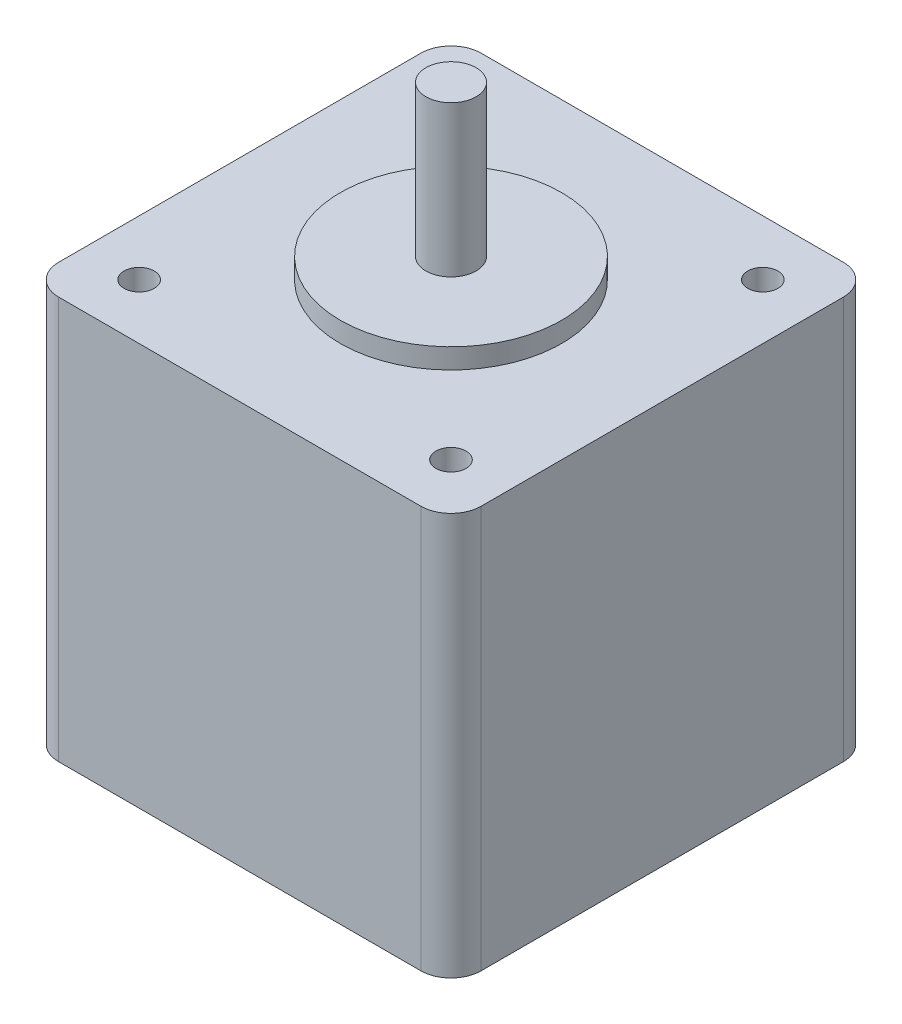
SolidWorks part; units mm, degrees
material "Rubber"
ref_plane "Front Plane" through (0, 0, 0) normal (0, 0, 1) x (1, 0, 0)
ref_plane "Top Plane" through (0, 0, 0) normal (0, 1, 0) x (1, 0, 0)
ref_plane "Right Plane" through (0, 0, 0) normal (1, 0, 0) x (0, 0, -1)
sketch "Sketch1" plane through (0, 0, 0) normal (0, 1, 0) x (1, 0, 0)
  line L1 (3, 0) -> (39, 0)
  line L2 (0, 3) -> (0, 39)
  line L3 (3, 42) -> (39, 42)
  line L4 (42, 3) -> (42, 39)
  arc A0 (39, 42) -> (42, 39) centre (39, 39) cw
  arc A1 (39, 0) -> (42, 3) centre (39, 3) ccw
  arc A2 (3, 0) -> (0, 3) centre (3, 3) cw
  arc A3 (0, 39) -> (3, 42) centre (3, 39) cw
  point P11 (0, 0)
  dimension "D1" = 3
extrude "Boss-Extrude1" add sketch "Sketch1" along normal blind 40
sketch "Sketch2" plane through (0, 40, 0) normal (0, 1, 0) x (1, 0, 0)
  line L1 (0, 39) -> (0, 3) construction
  line L2 (39, 42) -> (3, 42) construction
  circle A0 centre (21, 21) radius 11
  dimension "D1" = 21
  dimension "D2" = 21
extrude "Boss-Extrude2" add sketch "Sketch2" along normal blind 2
sketch "Sketch3" plane through (0, 42, 0) normal (0, 1, 0) x (1, 0, 0)
  circle A0 centre (21, 21) radius 2.5
extrude "Boss-Extrude3" add sketch "Sketch3" along normal blind 15
sketch "Sketch4" plane through (0, 40, 0) normal (0, 1, 0) x (1, 0, 0)
  line L2 (0, 39) -> (0, 3) construction
  line L4 (39, 42) -> (3, 42) construction
  circle A0 centre (5.5, 36.5) radius 1.5
  circle A1 centre (36.5, 36.5) radius 1.5
  circle A2 centre (36.5, 5.5) radius 1.5
  circle A3 centre (5.5, 5.5) radius 1.5
  dimension "D1" = 5.5
  dimension "D3" = 3
  dimension "D4" = 2
  dimension "D2" = 5.5
  dimension "D5" = 2
extrude "Cut-Extrude1" cut sketch "Sketch4" against normal blind 5
